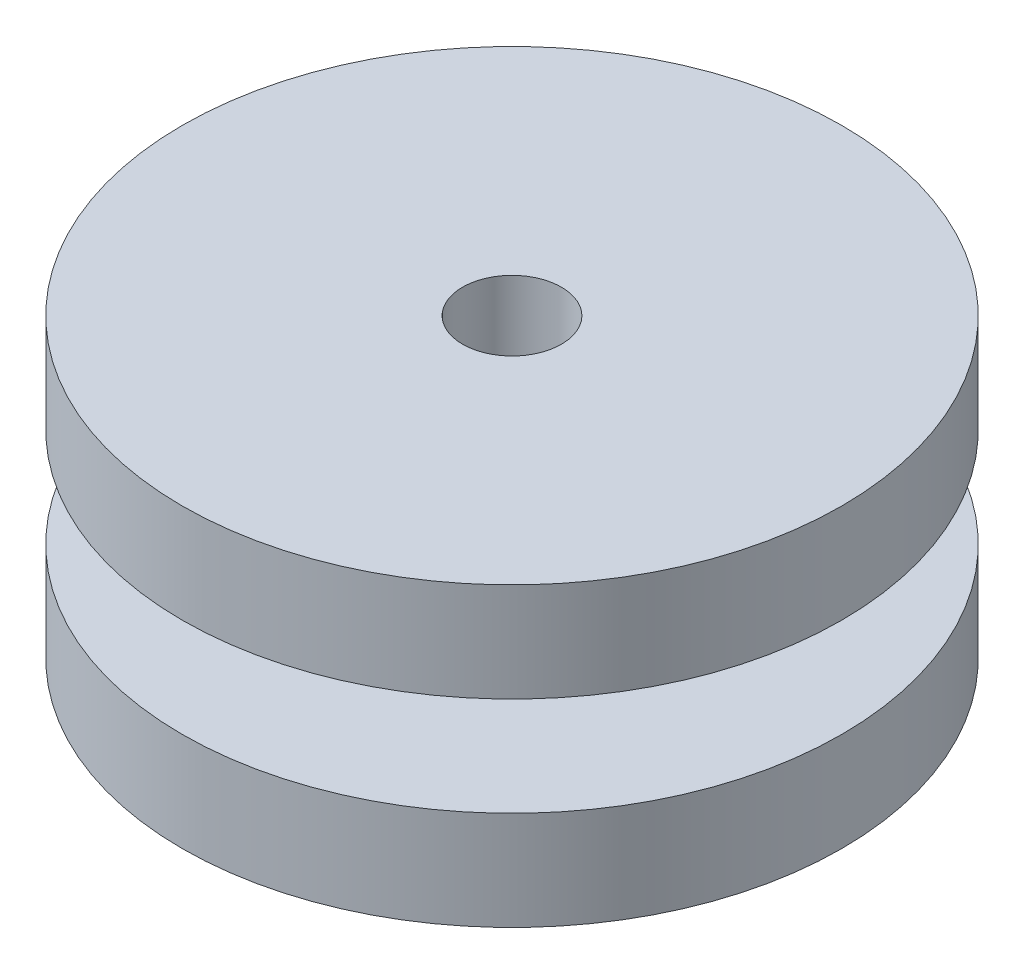
SolidWorks part; units mm, degrees
ref_plane "Front Plane" through (0, 0, 0) normal (0, 0, 1) x (1, 0, 0)
ref_plane "Top Plane" through (0, 0, 0) normal (0, 1, 0) x (1, 0, 0)
ref_plane "Right Plane" through (0, 0, 0) normal (1, 0, 0) x (0, 0, -1)
sketch "Sketch1" plane through (0, 0, 0) normal (0, 1, 0) x (1, 0, 0)
  circle A0 centre (0, 0) radius 1.5
  circle A1 centre (0, 0) radius 3.5
  dimension "D1" = 2
extrude "Boss-Extrude1" add sketch "Sketch1" along normal blind 9 contours A0 | A1
sketch "Sketch2" plane through (0, 9, 0) normal (0, 1, 0) x (1, 0, 0)
  circle A0 centre (0, 0) radius 1.5
  circle A1 centre (0, 0) radius 6
extrude "Boss-Extrude2" add sketch "Sketch2" against normal blind 3 contours A1 | A0
sketch "Sketch3" plane through (0, 0, 0) normal (0, -1, 0) x (1, 0, 0)
  circle A0 centre (0, 0) radius 1.5
  circle A1 centre (0, 0) radius 5
extrude "Boss-Extrude3" add sketch "Sketch3" against normal blind 3 contours A1 | A0
fillet "Fillet2" radius 1 2 edges at (0, 3, -3.5) (0, 6, 3.5)
sketch "Sketch4" plane through (0, 0, 0) normal (0, -1, 0) x (1, 0, 0)
  circle A0 centre (0, 0) radius 1.5
  circle A1 centre (0, 0) radius 10
extrude "Boss-Extrude4" add sketch "Sketch4" against normal blind 3 contours A1 | A0
sketch "Sketch5" plane through (0, 9, 0) normal (0, 1, 0) x (1, 0, 0)
  circle A0 centre (0, 0) radius 1.5
  circle A1 centre (0, 0) radius 10
extrude "Boss-Extrude5" add sketch "Sketch5" against normal blind 3 contours A1 | A0
